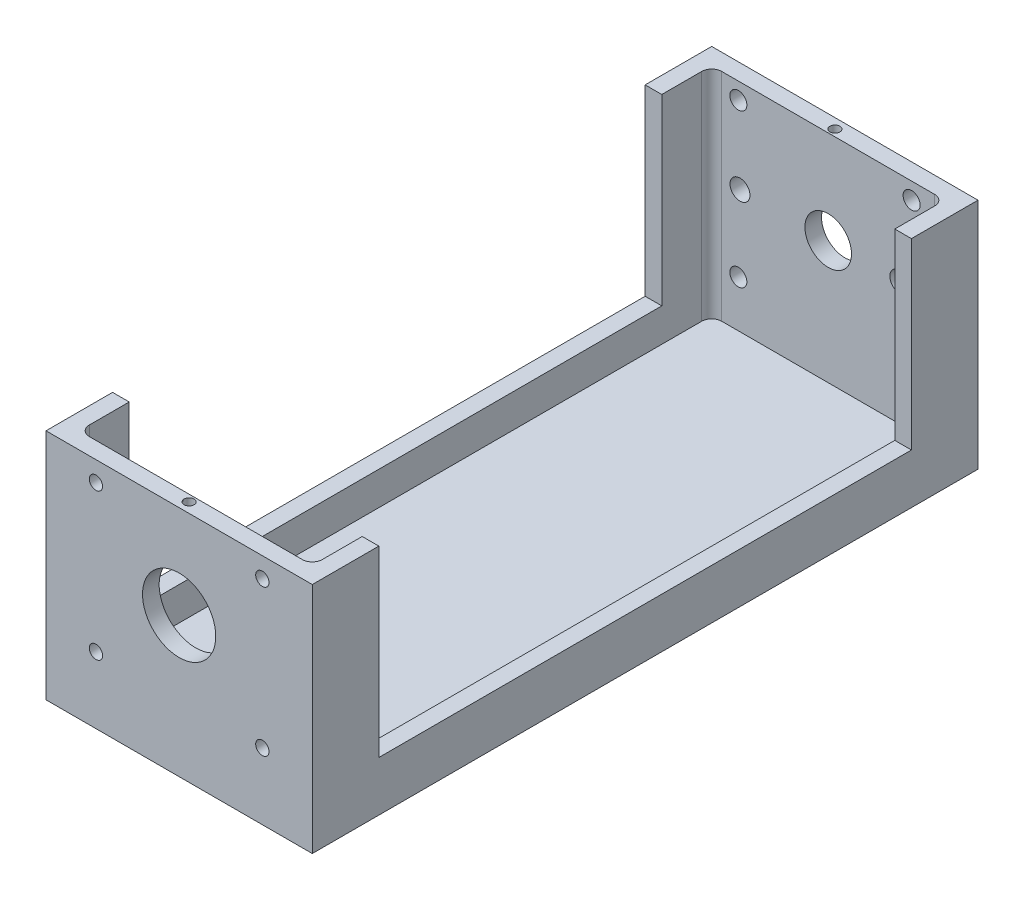
SolidWorks part; units mm, degrees
ref_plane "前视基准面" through (0, 0, 0) normal (0, 0, 1) x (1, 0, 0)
ref_plane "上视基准面" through (0, 0, 0) normal (0, 1, 0) x (1, 0, 0)
ref_plane "右视基准面" through (0, 0, 0) normal (1, 0, 0) x (0, 0, -1)
sketch "草图1" plane through (0, 0, 0) normal (0, 0, 1) x (1, 0, 0)
  line L1 (-40, -35) -> (40, -35)
  line L2 (-40, -35) -> (-40, 35)
  line L3 (-40, 35) -> (40, 35)
  line L4 (40, -35) -> (40, 35)
  line L5 (-40, -35) -> (40, 35) construction
  line L6 (-40, 35) -> (40, -35) construction
  point P0 (0, 0)
  dimension "D1" = 80
  dimension "D2" = 70
extrude "凸台-拉伸1" add sketch "草图1" against normal blind 200
sketch "草图2" plane through (0, 35, 0) normal (0, 1, 0) x (1, 0, 0)
  line L0 (-35, 192) -> (-35, 8)
  line L1 (-32, 5) -> (32, 5)
  line L2 (35, 8) -> (35, 192)
  line L3 (32, 195) -> (-32, 195)
  line L4 (-40, 0) -> (40, 0)
  line L5 (40, 0) -> (40, 200)
  line L6 (40, 200) -> (-40, 200)
  line L7 (-40, 200) -> (-40, 0)
  line L8 (-40, 0) -> (40, 0)
  line L9 (40, 0) -> (40, 200)
  line L10 (40, 200) -> (-40, 200)
  line L11 (-40, 200) -> (-40, 0)
  line L12 (-35, 5) -> (35, 5) construction
  line L13 (35, 5) -> (35, 195) construction
  line L14 (-35, 195) -> (-35, 5) construction
  line L15 (35, 195) -> (-35, 195) construction
  arc A0 (32, 5) -> (35, 8) centre (32, 8) ccw
  arc A1 (-35, 8) -> (-32, 5) centre (-32, 8) ccw
  arc A2 (35, 192) -> (32, 195) centre (32, 192) ccw
  arc A3 (-35, 192) -> (-32, 195) centre (-32, 192) cw
  dimension "D3" = 3
  dimension "D1" = 0
  dimension "D2" = 5
extrude "切除-拉伸1" cut sketch "草图2" against normal blind 65 contours A3 L0 A1 L1 A0 L2 A2 L3
sketch "草图3" plane through (0, 0, 0) normal (0, 0, 1) x (1, 0, 0)
  line L0 (0, 0) -> (0, 37.0041) construction
  line L1 (-40, -29) -> (40, -29) construction
  line L2 (-40, 35) -> (-40, -35) construction
  line L3 (40, -35) -> (40, 35) construction
  line L4 (-40, -35) -> (40, -35) construction
  line L5 (40, 35) -> (-40, 35) construction
  line L6 (-34, -29) -> (40, -29) construction
  line L9 (0, 7) -> (0, 35) construction
  line L10 (-26, 7) -> (26, 7) construction
  circle A0 centre (-26, 7) radius 3.5 construction
  circle A1 centre (0, 7) radius 11
  circle A2 centre (26, 7) radius 3.5 construction
  dimension "D2" = 7
  dimension "D3" = 22
  dimension "D4" = 7
  dimension "D1" = 6
  dimension "D5" = 28
  dimension "D6" = 26
  dimension "D7" = 26
extrude "切除-拉伸2" cut sketch "草图3" against normal blind 10
sketch "草图4" plane through (-40, 0, 0) normal (-1, 0, 0) x (0, 0, 1)
  line L0 (-126.5, -4) -> (-153.5, -4)
  line L1 (-126.5, -4) -> (-126.5, 32)
  line L2 (-126.5, 32) -> (-153.5, 32)
  line L3 (-153.5, -4) -> (-153.5, 32)
  line L4 (-140, -1.9135) -> (-140, 22.4271) construction
  line L5 (-200, 35) -> (0, 35) construction
  line L6 (-200, 35) -> (-200, -35) construction
  circle A0 centre (-121.5, 2) radius 2
  circle A1 centre (-121.5, 26) radius 2
  circle A2 centre (-158.5, 26) radius 2
  circle A3 centre (-158.5, 2) radius 2
  dimension "D1" = 4
  dimension "D2" = 4
  dimension "D3" = 36
  dimension "D4" = 6
  dimension "D5" = 5
  dimension "D6" = 6
  dimension "D7" = 5
  dimension "D8" = 27
  dimension "D9" = 3
  dimension "D10" = 60
extrude "切除-拉伸3" cut sketch "草图4" against normal blind 10
sketch "草图6" plane through (0, -30, 0) normal (0, 1, 0) x (1, 0, 0)
  line L0 (-17, 114) -> (-17, 167) construction
  line L1 (-17, 140.5) -> (-23.7867, 140.5) construction
  line L2 (-35, 192) -> (-35, 8) construction
  line L3 (32, 195) -> (-32, 195) construction
  circle A0 centre (-17, 167) radius 3.5
  circle A1 centre (-17, 114) radius 3.5
  dimension "D2" = 7
  dimension "D5" = 7
  dimension "D1" = 53
  dimension "D3" = 18
  dimension "D4" = 54.5
extrude "切除-拉伸5" [suppressed] cut sketch "草图6" against normal blind 10
sketch "草图7" plane through (0, 35, 0) normal (0, 1, 0) x (1, 0, 0)
  line L0 (0, -10.1016) -> (0, 210.5413) construction
  line L1 (40, 0) -> (-40, 0) construction
  line L2 (40, 200) -> (40, 0) construction
  line L3 (-40, 200) -> (-40, 0) construction
  line L4 (40, 200) -> (-40, 200) construction
  circle A0 centre (-37, 150) radius 1.5
  circle A1 centre (-37, 50) radius 1.5
  circle A2 centre (37, 50) radius 1.5
  circle A3 centre (37, 150) radius 1.5
  circle A4 centre (0, 197) radius 1.5
  circle A5 centre (0, 3) radius 1.5
  dimension "D1" = 100
  dimension "D3" = 50
  dimension "D5" = 3
  dimension "D6" = 3
  dimension "D7" = 3
  dimension "D8" = 3
  dimension "D9" = 3
  dimension "D10" = 3
  dimension "D11" = 3
  dimension "D12" = 3
  dimension "D14" = 3
  dimension "D15" = 3
  dimension "D16" = 3
  dimension "D2" = 100
  dimension "D4" = 50
  dimension "D13" = 3
extrude "切除-拉伸6" cut sketch "草图7" against normal blind 10
sketch "草图8" plane through (40, 0, 0) normal (1, 0, 0) x (0, 0, -1)
  line L0 (200, 35) -> (0, 35) construction
  line L1 (20, 35) -> (180, 35)
  line L2 (20, 35) -> (20, -20)
  line L3 (20, -20) -> (180, -20)
  line L4 (180, 35) -> (180, -20)
  line L5 (20, 35) -> (180, -20) construction
  line L6 (20, -20) -> (180, 35) construction
  line L7 (0, -35) -> (0, 35) construction
  dimension "D1" = 160
  dimension "D2" = 55
  dimension "D3" = 20
extrude "切除-拉伸7" cut sketch "草图8" against normal through all
sketch "草图10" plane through (0, 0, -200) normal (0, 0, -1) x (-1, 0, 0)
  circle A0 centre (0, 7) radius 11 construction
  circle A1 centre (0, 7) radius 11 construction
  circle A2 centre (0, 7) radius 7
  dimension "D1" = 14
extrude "切除-拉伸9" cut sketch "草图10" against normal blind 10
sketch "草图11" plane through (0, 0, -200) normal (0, 0, -1) x (-1, 0, 0)
  circle A0 centre (-21.5, 7) radius 3 construction
  circle A1 centre (26.5, 7) radius 3 construction
  circle A2 centre (-21.5, 7) radius 3
  circle A3 centre (26.5, 7) radius 3
extrude "切除-拉伸10" cut sketch "草图11" against normal blind 10
sketch "草图12" plane through (0, 0, -200) normal (0, 0, -1) x (-1, 0, 0)
  circle A0 centre (-25.0526, -16) radius 2.5551 construction
  circle A1 centre (-25.0526, 30) radius 2.5551 construction
  circle A2 centre (27, 30) radius 2.5551 construction
  circle A3 centre (27, -16) radius 2.5551 construction
  circle A4 centre (-25.0526, -16) radius 2.5551
  circle A5 centre (-25.0526, 30) radius 2.5551
  circle A6 centre (27, 30) radius 2.5551
  circle A7 centre (27, -16) radius 2.5551
extrude "切除-拉伸11" cut sketch "草图12" against normal blind 10
sketch "草图13" plane through (0, 0, 0) normal (0, 0, 1) x (1, 0, 0)
  circle A0 centre (25, -15) radius 2 construction
  circle A1 centre (25, 29) radius 2 construction
  circle A2 centre (-25, 29) radius 2 construction
  circle A3 centre (-25, -15) radius 2 construction
  circle A4 centre (25, -15) radius 2
  circle A5 centre (25, 29) radius 2
  circle A6 centre (-25, 29) radius 2
  circle A7 centre (-25, -15) radius 2
extrude "切除-拉伸12" cut sketch "草图13" against normal blind 20
